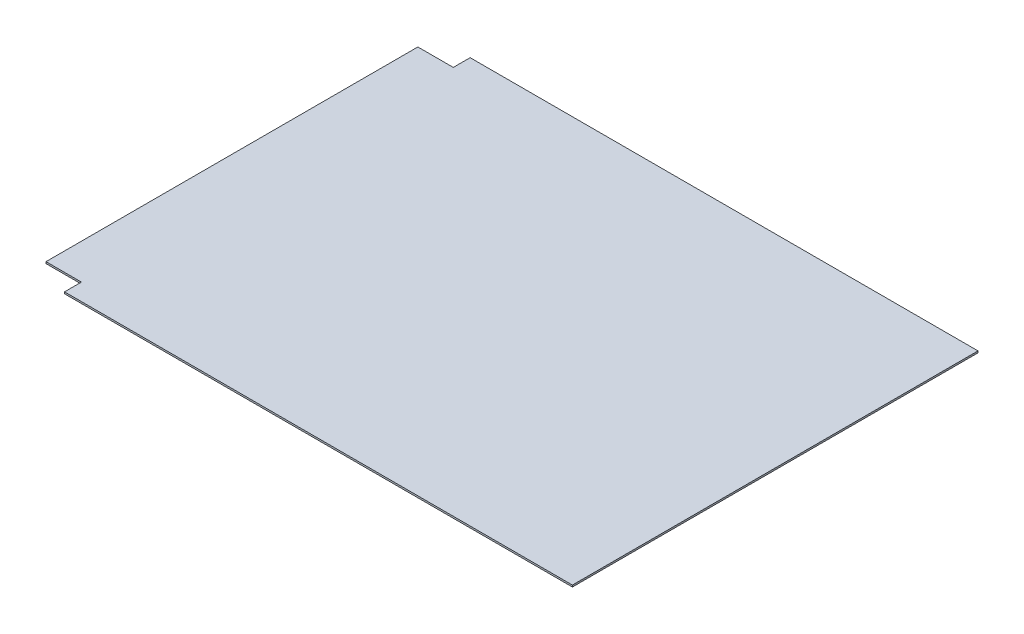
SolidWorks part; units mm, degrees
material "Galvanized Steel"
ref_plane "Front Plane" through (0, 0, 0) normal (0, 0, 1) x (1, 0, 0)
ref_plane "Top Plane" through (0, 0, 0) normal (0, 1, 0) x (1, 0, 0)
ref_plane "Right Plane" through (0, 0, 0) normal (1, 0, 0) x (0, 0, -1)
sketch "Sketch1" plane through (0, 0, 0) normal (0, 1, 0) x (1, 0, 0)
  line L0 (-382.408, 0) -> (-382.408, 12.7)
  line L1 (0, 0) -> (-382.408, 0)
  line L2 (0, 0) -> (0, 305.4)
  line L3 (0, 305.4) -> (-382.408, 305.4)
  line L4 (-409.078, 12.7) -> (-409.078, 292.7)
  line L5 (-382.408, 12.7) -> (-409.078, 12.7)
  line L6 (-382.408, 305.4) -> (-382.408, 292.7)
  line L7 (-382.408, 292.7) -> (-409.078, 292.7)
  dimension "D1" = 409.078
  dimension "D2" = 305.4
  dimension "D3" = 12.7
  dimension "D4" = 26.67
  dimension "D5" = 12.7
  dimension "D6" = 26.67
extrude "Boss-Extrude1" add sketch "Sketch1" along normal blind 1.3106
